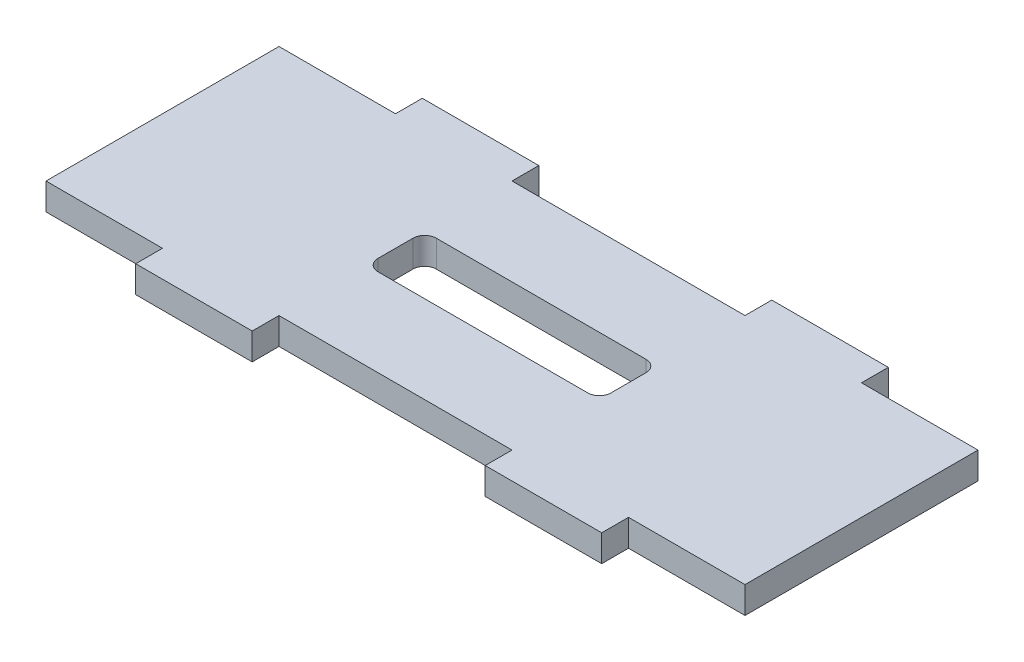
SolidWorks part; units mm, degrees
ref_plane "Front Plane" through (0, 0, 0) normal (0, 0, 1) x (1, 0, 0)
ref_plane "Top Plane" through (0, 0, 0) normal (0, 1, 0) x (1, 0, 0)
ref_plane "Right Plane" through (0, 0, 0) normal (1, 0, 0) x (0, 0, -1)
sketch "Sketch1" plane through (0, 0, 0) normal (0, 1, 0) x (1, 0, 0)
  line L0 (0, 0) -> (60, 0) construction
  line L1 (0, 0) -> (0, 20)
  line L2 (0, -2.3) -> (60, -2.3) construction
  line L3 (0, 0) -> (0, -2.3) construction
  line L4 (0, 20) -> (0, 22.3) construction
  line L5 (0, 20) -> (60, 20) construction
  line L6 (60, 20) -> (60, 0)
  line L7 (0, 22.3) -> (60, 22.3) construction
  line L8 (60, 22.3) -> (60, 20) construction
  line L9 (60, -2.3) -> (60, 0) construction
  line L10 (30, -2.3) -> (20, -2.3) construction
  line L11 (30, -2.3) -> (40, -2.3) construction
  line L12 (20, -2.3) -> (10, -2.3) construction
  line L13 (40, -2.3) -> (50, -2.3) construction
  line L14 (10, -2.3) -> (10, 22.3) construction
  line L15 (20, -2.3) -> (20, 22.3) construction
  line L16 (40, -2.3) -> (40, 22.3) construction
  line L17 (50, -2.3) -> (50, 22.3) construction
  line L18 (0, 20) -> (10, 20)
  line L19 (10, 20) -> (10, 22.3)
  line L20 (10, 22.3) -> (20, 22.3)
  line L21 (20, 22.3) -> (20, 20)
  line L22 (20, 20) -> (40, 20)
  line L23 (40, 20) -> (40, 22.3)
  line L24 (40, 22.3) -> (50, 22.3)
  line L25 (50, 22.3) -> (50, 20)
  line L26 (50, 20) -> (60, 20)
  line L27 (0, 0) -> (10, 0)
  line L28 (10, 0) -> (10, -2.3)
  line L29 (10, -2.3) -> (20, -2.3)
  line L30 (20, -2.3) -> (20, 0)
  line L31 (20, 0) -> (40, 0)
  line L32 (40, 0) -> (40, -2.3)
  line L33 (40, -2.3) -> (50, -2.3)
  line L34 (50, -2.3) -> (50, 0)
  line L35 (50, 0) -> (60, 0)
  dimension "D1" = 60
  dimension "D2" = 20
  dimension "D3" = 10
  dimension "D4" = 2.3
  dimension "D5" = 2.3
  dimension "D6" = 10
  dimension "D7" = 10
  dimension "D8" = 10
extrude "Boss-Extrude1" add sketch "Sketch1" along normal blind 2.3
sketch "Sketch2" plane through (0, 2.3, 0) normal (0, 1, 0) x (1, 0, 0)
  line L0 (0, 10) -> (60, 10) construction
  line L1 (0, 20) -> (0, 0) construction
  line L2 (60, 0) -> (60, 20) construction
  line L3 (0, 10) -> (0, 7.5) construction
  line L4 (0, 7.5) -> (60, 7.5) construction
  line L5 (0, 10) -> (0, 12.5) construction
  line L6 (0, 12.5) -> (60, 12.5) construction
  line L7 (0, 12.5) -> (20, 12.5) construction
  line L8 (0, 12.5) -> (40, 12.5) construction
  line L9 (20, 12.5) -> (20, 7.5)
  line L10 (40, 12.5) -> (40, 7.5)
  line L11 (20, 12.5) -> (40, 12.5)
  line L12 (20, 7.5) -> (40, 7.5)
  dimension "D1" = 2.5
  dimension "D2" = 2.5
  dimension "D3" = 20
  dimension "D4" = 40
extrude "Cut-Extrude1" cut sketch "Sketch2" against normal blind 10
fillet "Fillet1" radius 1 4 edges at (40, 1.15, -7.5) (40, 1.15, -12.5) (20, 1.15, -7.5) (20, 1.15, -12.5)
